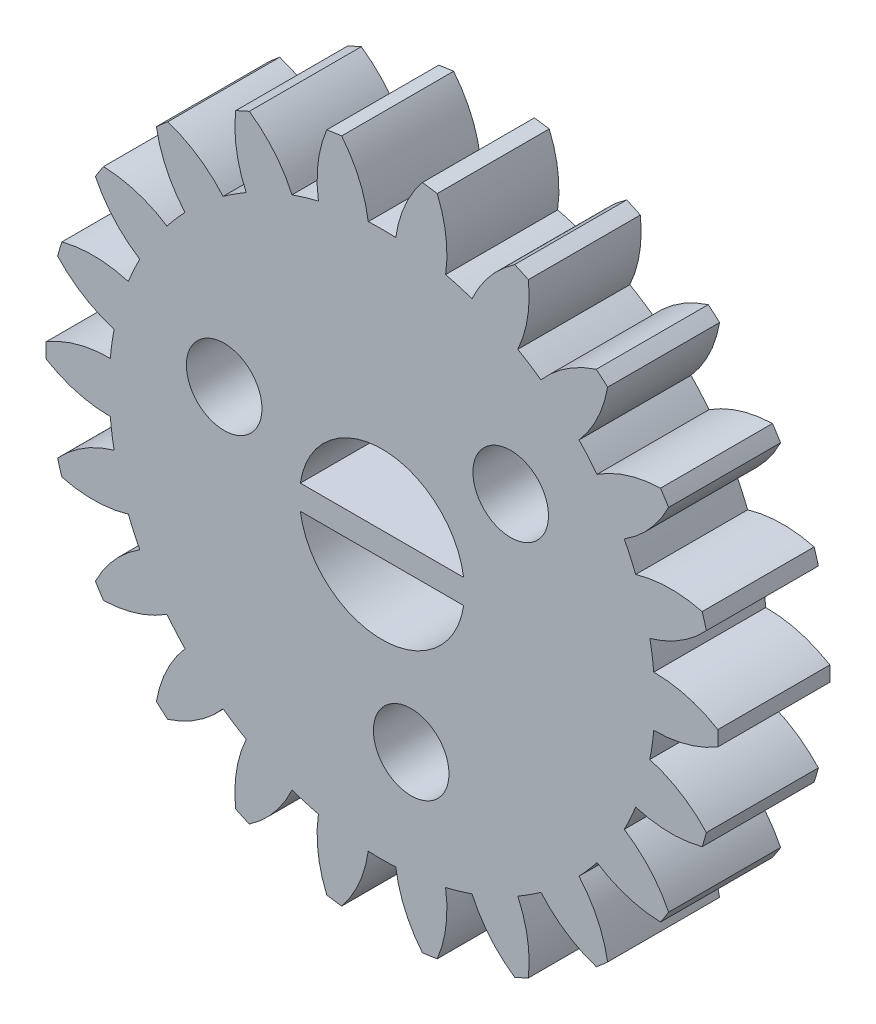
SolidWorks part; units mm, degrees
ref_plane "Front Plane" through (0, 0, 0) normal (0, 0, 1) x (1, 0, 0)
ref_plane "Top Plane" through (0, 0, 0) normal (0, 1, 0) x (1, 0, 0)
ref_plane "Right Plane" through (0, 0, 0) normal (1, 0, 0) x (0, 0, -1)
sketch "Model" plane through (0, 0, 0) normal (0, 0, 1) x (1, 0, 0)
  circle A0 centre (0, 0) radius 2.5
  arc A1 (-11.997, 0.2683) -> (-11.997, -0.2683) centre (0, 0) ccw
  arc A2 (-9.7074, 0.8997) -> (-11.997, 0.2683) centre (-9.7259, -3.5003) ccw
  arc A3 (-9.5676, 1.8717) -> (-9.7074, 0.8997) centre (0, 0) ccw
  arc A4 (-11.5866, 3.1225) -> (-9.5676, 1.8717) centre (-8.3458, 6.0986) ccw
  arc A5 (-11.4355, 3.6374) -> (-11.5866, 3.1225) centre (0, 0) ccw
  arc A6 (-9.0607, 3.5981) -> (-11.4355, 3.6374) centre (-10.3181, -0.6184) ccw
  arc A7 (-8.6528, 4.4914) -> (-9.0607, 3.5981) centre (0, 0) ccw
  arc A8 (-10.2376, 6.2604) -> (-8.6528, 4.4914) centre (-6.2896, 8.2029) ccw
  arc A9 (-9.9475, 6.7118) -> (-10.2376, 6.2604) centre (0, 0) ccw
  arc A10 (-7.68, 6.0051) -> (-9.9475, 6.7118) centre (-10.0744, 2.3136) ccw
  arc A11 (-7.0369, 6.7472) -> (-7.68, 6.0051) centre (0, 0) ccw
  arc A12 (-8.0591, 8.891) -> (-7.0369, 6.7472) centre (-3.7238, 9.6426) ccw
  arc A13 (-7.6536, 9.2424) -> (-8.0591, 8.891) centre (0, 0) ccw
  arc A14 (-5.6771, 7.9255) -> (-7.6536, 9.2424) centre (-9.0145, 5.0582) ccw
  arc A15 (-4.851, 8.4564) -> (-5.6771, 7.9255) centre (0, 0) ccw
  arc A16 (-5.2278, 10.8014) -> (-4.851, 8.4564) centre (-0.8563, 10.3011) ccw
  arc A17 (-4.7397, 11.0243) -> (-5.2278, 10.8014) centre (0, 0) ccw
  arc A18 (-3.2142, 9.2039) -> (-4.7397, 11.0243) centre (-7.2243, 7.3929) ccw
  arc A19 (-2.272, 9.4806) -> (-3.2142, 9.2039) centre (0, 0) ccw
  arc A20 (-1.9729, 11.8367) -> (-2.272, 9.4806) centre (2.0805, 10.1251) ccw
  arc A21 (-1.4418, 11.9131) -> (-1.9729, 11.8367) centre (0, 0) ccw
  arc A22 (-0.491, 9.7366) -> (-1.4418, 11.9131) centre (-4.8488, 9.1288) ccw
  arc A23 (0.491, 9.7366) -> (-0.491, 9.7366) centre (0, 0) ccw
  arc A24 (1.4418, 11.9131) -> (0.491, 9.7366) centre (4.8488, 9.1288) ccw
  arc A25 (1.9729, 11.8367) -> (1.4418, 11.9131) centre (0, 0) ccw
  arc A26 (2.272, 9.4806) -> (1.9729, 11.8367) centre (-2.0805, 10.1251) ccw
  arc A27 (3.2142, 9.2039) -> (2.272, 9.4806) centre (0, 0) ccw
  arc A28 (4.7397, 11.0243) -> (3.2142, 9.2039) centre (7.2243, 7.3929) ccw
  arc A29 (5.2278, 10.8014) -> (4.7397, 11.0243) centre (0, 0) ccw
  arc A30 (4.851, 8.4564) -> (5.2278, 10.8014) centre (0.8563, 10.3011) ccw
  arc A31 (5.6771, 7.9255) -> (4.851, 8.4564) centre (0, 0) ccw
  arc A32 (7.6536, 9.2424) -> (5.6771, 7.9255) centre (9.0145, 5.0582) ccw
  arc A33 (8.0591, 8.891) -> (7.6536, 9.2424) centre (0, 0) ccw
  arc A34 (7.0369, 6.7472) -> (8.0591, 8.891) centre (3.7238, 9.6426) ccw
  arc A35 (7.68, 6.0051) -> (7.0369, 6.7472) centre (0, 0) ccw
  arc A36 (9.9475, 6.7118) -> (7.68, 6.0051) centre (10.0744, 2.3136) ccw
  arc A37 (10.2376, 6.2604) -> (9.9475, 6.7118) centre (0, 0) ccw
  arc A38 (8.6528, 4.4914) -> (10.2376, 6.2604) centre (6.2896, 8.2029) ccw
  arc A39 (9.0607, 3.5981) -> (8.6528, 4.4914) centre (0, 0) ccw
  arc A40 (11.4355, 3.6374) -> (9.0607, 3.5981) centre (10.3181, -0.6184) ccw
  arc A41 (11.5866, 3.1225) -> (11.4355, 3.6374) centre (0, 0) ccw
  arc A42 (9.5676, 1.8717) -> (11.5866, 3.1225) centre (8.3458, 6.0986) ccw
  arc A43 (9.7074, 0.8997) -> (9.5676, 1.8717) centre (0, 0) ccw
  arc A44 (11.997, 0.2683) -> (9.7074, 0.8997) centre (9.7259, -3.5003) ccw
  arc A45 (11.997, -0.2683) -> (11.997, 0.2683) centre (0, 0) ccw
  arc A46 (9.7074, -0.8997) -> (11.997, -0.2683) centre (9.7259, 3.5003) ccw
  arc A47 (9.5676, -1.8717) -> (9.7074, -0.8997) centre (0, 0) ccw
  arc A48 (11.5866, -3.1225) -> (9.5676, -1.8717) centre (8.3458, -6.0986) ccw
  arc A49 (11.4355, -3.6374) -> (11.5866, -3.1225) centre (0, 0) ccw
  arc A50 (9.0607, -3.5981) -> (11.4355, -3.6374) centre (10.3181, 0.6184) ccw
  arc A51 (8.6528, -4.4914) -> (9.0607, -3.5981) centre (0, 0) ccw
  arc A52 (10.2376, -6.2604) -> (8.6528, -4.4914) centre (6.2896, -8.2029) ccw
  arc A53 (9.9475, -6.7118) -> (10.2376, -6.2604) centre (0, 0) ccw
  arc A54 (7.68, -6.0051) -> (9.9475, -6.7118) centre (10.0744, -2.3136) ccw
  arc A55 (7.0369, -6.7472) -> (7.68, -6.0051) centre (0, 0) ccw
  arc A56 (8.0591, -8.891) -> (7.0369, -6.7472) centre (3.7238, -9.6426) ccw
  arc A57 (7.6536, -9.2424) -> (8.0591, -8.891) centre (0, 0) ccw
  arc A58 (5.6771, -7.9255) -> (7.6536, -9.2424) centre (9.0145, -5.0582) ccw
  arc A59 (4.851, -8.4564) -> (5.6771, -7.9255) centre (0, 0) ccw
  arc A60 (5.2278, -10.8014) -> (4.851, -8.4564) centre (0.8563, -10.3011) ccw
  arc A61 (4.7397, -11.0243) -> (5.2278, -10.8014) centre (0, 0) ccw
  arc A62 (3.2142, -9.2039) -> (4.7397, -11.0243) centre (7.2243, -7.3929) ccw
  arc A63 (2.272, -9.4806) -> (3.2142, -9.2039) centre (0, 0) ccw
  arc A64 (1.9729, -11.8367) -> (2.272, -9.4806) centre (-2.0805, -10.1251) ccw
  arc A65 (1.4418, -11.9131) -> (1.9729, -11.8367) centre (0, 0) ccw
  arc A66 (0.491, -9.7366) -> (1.4418, -11.9131) centre (4.8488, -9.1288) ccw
  arc A67 (-0.491, -9.7366) -> (0.491, -9.7366) centre (0, 0) ccw
  arc A68 (-1.4418, -11.9131) -> (-0.491, -9.7366) centre (-4.8488, -9.1288) ccw
  arc A69 (-1.9729, -11.8367) -> (-1.4418, -11.9131) centre (0, 0) ccw
  arc A70 (-2.272, -9.4806) -> (-1.9729, -11.8367) centre (2.0805, -10.1251) ccw
  arc A71 (-3.2142, -9.2039) -> (-2.272, -9.4806) centre (0, 0) ccw
  arc A72 (-4.7397, -11.0243) -> (-3.2142, -9.2039) centre (-7.2243, -7.3929) ccw
  arc A73 (-5.2278, -10.8014) -> (-4.7397, -11.0243) centre (0, 0) ccw
  arc A74 (-4.851, -8.4564) -> (-5.2278, -10.8014) centre (-0.8563, -10.3011) ccw
  arc A75 (-5.6771, -7.9255) -> (-4.851, -8.4564) centre (0, 0) ccw
  arc A76 (-7.6536, -9.2424) -> (-5.6771, -7.9255) centre (-9.0145, -5.0582) ccw
  arc A77 (-8.0591, -8.891) -> (-7.6536, -9.2424) centre (0, 0) ccw
  arc A78 (-7.0369, -6.7472) -> (-8.0591, -8.891) centre (-3.7238, -9.6426) ccw
  arc A79 (-7.68, -6.0051) -> (-7.0369, -6.7472) centre (0, 0) ccw
  arc A80 (-9.9475, -6.7118) -> (-7.68, -6.0051) centre (-10.0744, -2.3136) ccw
  arc A81 (-10.2376, -6.2604) -> (-9.9475, -6.7118) centre (0, 0) ccw
  arc A82 (-8.6528, -4.4914) -> (-10.2376, -6.2604) centre (-6.2896, -8.2029) ccw
  arc A83 (-9.0607, -3.5981) -> (-8.6528, -4.4914) centre (0, 0) ccw
  arc A84 (-11.4355, -3.6374) -> (-9.0607, -3.5981) centre (-10.3181, 0.6184) ccw
  arc A85 (-11.5866, -3.1225) -> (-11.4355, -3.6374) centre (0, 0) ccw
  arc A86 (-9.5676, -1.8717) -> (-11.5866, -3.1225) centre (-8.3458, -6.0986) ccw
  arc A87 (-9.7074, -0.8997) -> (-9.5676, -1.8717) centre (0, 0) ccw
  arc A88 (-11.997, -0.2683) -> (-9.7074, -0.8997) centre (-9.7259, 3.5003) ccw
extrude "Boss-Extrude1" add sketch "Model" along normal blind 4
sketch "Sketch4" plane through (0, 0, 0) normal (0, 0, 1) x (1, 0, 0)
  circle A0 centre (0, 0) radius 11 construction
  dimension "D1" = 22
sketch "Sketch2" plane through (0, 0, 4) normal (0, 0, 1) x (1, 0, 0)
  circle A0 centre (0, 0) radius 2.95
  dimension "D1" = 5.9
extrude "Cut-Extrude1" cut sketch "Sketch2" against normal blind 4
sketch "Sketch3" plane through (0, 0, 4) normal (0, 0, 1) x (1, 0, 0)
  line L0 (0, 0) -> (-9.3925, 0) construction
  line L1 (0, 0) -> (-5.6382, 2.0521) construction
  circle A0 centre (-5.6382, 2.0521) radius 1.35
  dimension "D1" = 2.7
  dimension "D2" = 6
  dimension "D3" = 20
extrude "Cut-Extrude2" cut sketch "Sketch3" against normal blind 4
pattern_circular "CirPattern1" count 3 over 360 about axis through (0, 0, 0) along (0, 0, 1) of "Cut-Extrude2"
sketch "Sketch5" plane through (0, 0, 0) normal (0, 0, 1) x (1, 0, 0)
  line L1 (-3, -0.435) -> (3, -0.435)
  line L2 (-3, -0.435) -> (-3, 0.435)
  line L3 (-3, 0.435) -> (3, 0.435)
  line L4 (3, -0.435) -> (3, 0.435)
  line L5 (0, 0.435) -> (0, -0.435) construction
  line L6 (-3, 0) -> (3, 0) construction
  point P0 (0, 0)
  dimension "D1" = 0.87
  dimension "D2" = 6
extrude "Boss-Extrude2" add sketch "Sketch5" along normal blind 4
